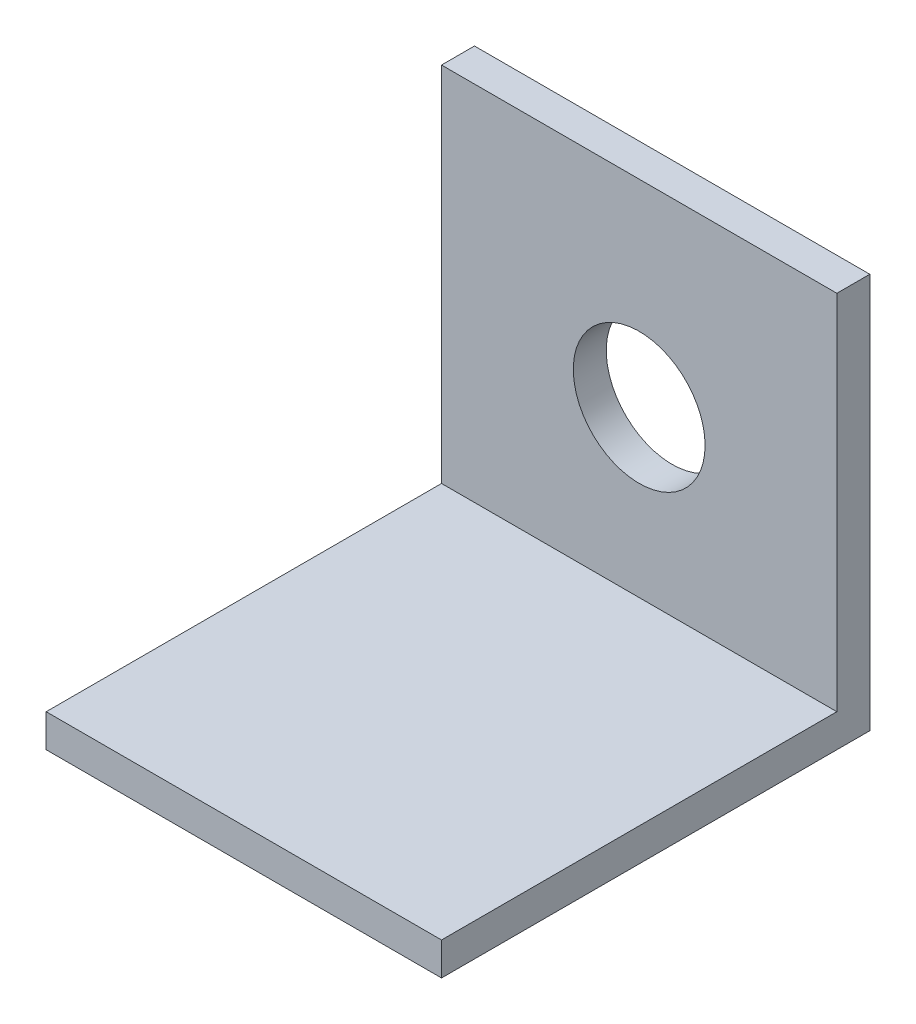
SolidWorks part; units mm, degrees
ref_plane "Front Plane" through (0, 0, 0) normal (0, 0, 1) x (1, 0, 0)
ref_plane "Top Plane" through (0, 0, 0) normal (0, 1, 0) x (1, 0, 0)
ref_plane "Right Plane" through (0, 0, 0) normal (1, 0, 0) x (0, 0, -1)
sketch "Sketch1" plane through (0, 0, 0) normal (0, 0, 1) x (1, 0, 0)
  line L1 (-9.525, 9.525) -> (9.525, 9.525)
  line L2 (-9.525, 9.525) -> (-9.525, -9.525)
  line L3 (-9.525, -9.525) -> (9.525, -9.525)
  line L4 (9.525, 9.525) -> (9.525, -9.525)
  line L5 (-9.525, 9.525) -> (9.525, -9.525) construction
  line L6 (-9.525, -9.525) -> (9.525, 9.525) construction
  circle A0 centre (0, 0) radius 3.175
  point P1 (0, 0)
extrude "Boss-Extrude1" add sketch "Sketch1" along normal mid plane 1.5875
sketch "Sketch2" plane through (0, -9.525, 0) normal (0, -1, 0) x (1, 0, 0)
  line L0 (-9.525, 0.7937) -> (9.525, 0.7937)
  line L1 (-9.525, 0.7937) -> (-9.525, 19.8438)
  line L2 (9.525, 0.7937) -> (9.525, 19.8438)
  line L3 (-9.525, 19.8438) -> (9.525, 19.8438)
extrude "Boss-Extrude2" add sketch "Sketch2" against normal blind 1.5875
